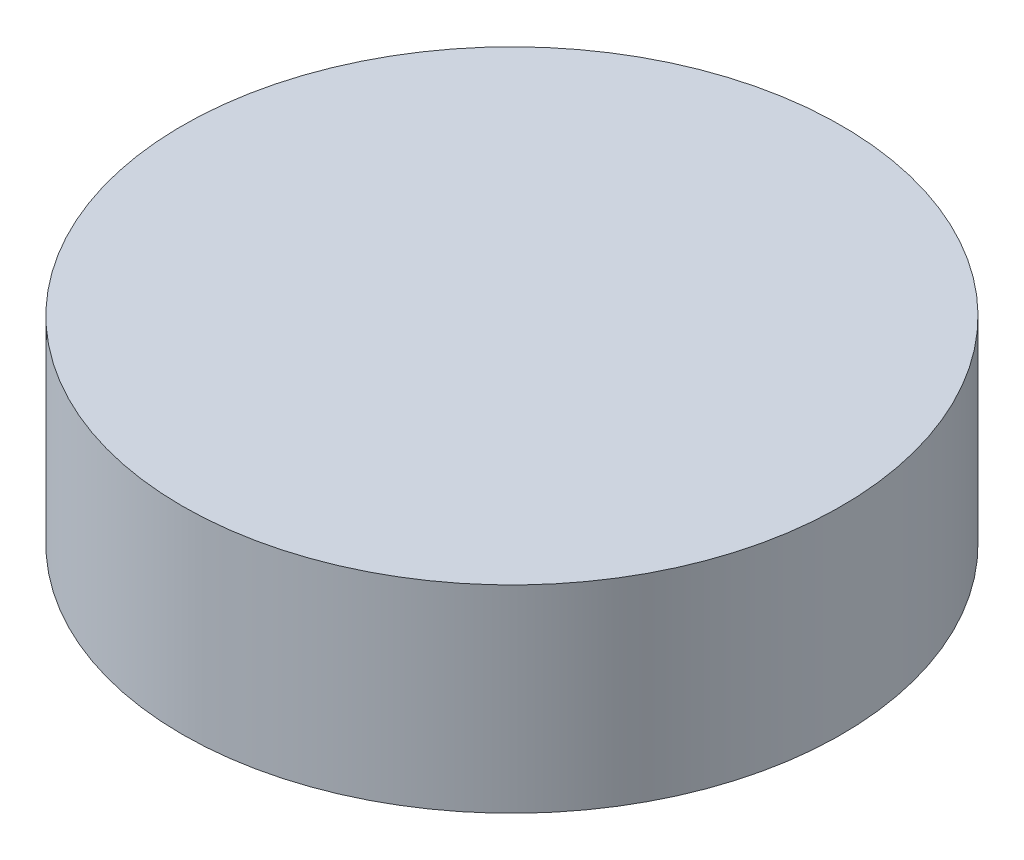
SolidWorks part; units mm, degrees
ref_plane "Plan de face" through (0, 0, 0) normal (0, 0, 1) x (1, 0, 0)
ref_plane "Plan de dessus" through (0, 0, 0) normal (0, 1, 0) x (1, 0, 0)
ref_plane "Plan de droite" through (0, 0, 0) normal (1, 0, 0) x (0, 0, -1)
sketch "Esquisse1" plane through (0, 0, 0) normal (0, 1, 0) x (1, 0, 0)
  circle A0 centre (0, 0) radius 40
  dimension "D1" = 80
extrude "Boss.-Extru.1" add sketch "Esquisse1" along normal blind 24
